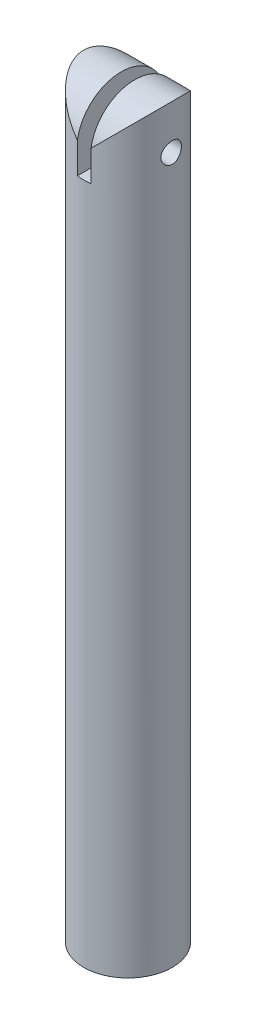
SolidWorks part; units mm, degrees
ref_plane "Front Plane" through (0, 0, 0) normal (0, 0, 1) x (1, 0, 0)
ref_plane "Top Plane" through (0, 0, 0) normal (0, 1, 0) x (1, 0, 0)
ref_plane "Right Plane" through (0, 0, 0) normal (1, 0, 0) x (0, 0, -1)
sketch "Sketch1" plane through (0, 0, 0) normal (0, 1, 0) x (1, 0, 0)
  circle A0 centre (0, 0) radius 2.5
  circle A1 centre (0, 0) radius 6.5
  dimension "D1" = 5
  dimension "D2" = 13
extrude "Boss-Extrude1" add sketch "Sketch1" along normal blind 100
sketch "Sketch2" plane through (0, 100, 0) normal (0, 1, 0) x (1, 0, 0)
  circle A0 centre (0, 0) radius 6.5
extrude "Boss-Extrude2" add sketch "Sketch2" against normal blind 10
sketch "Sketch3" plane through (0, 100, 0) normal (0, 1, 0) x (1, 0, 0)
  line L2 (-1, -6.4226) -> (-1, 6.4226)
  line L4 (1, -6.4226) -> (1, 6.4226)
  arc A0 (1, -6.4226) -> (1, 6.4226) centre (0, 0) ccw
  arc A2 (-1, 6.4226) -> (-1, -6.4226) centre (0, 0) ccw
  point P0 (0, 0)
extrude "Boss-Extrude3" add sketch "Sketch3" along normal blind 10
sketch "Sketch4" plane through (0, 0, 0) normal (1, 0, 0) x (0, 0, -1)
  line L0 (-6.5, 103.5) -> (6.5, 103.5)
  line L1 (6.4226, 110) -> (-6.4226, 110) construction
  line L2 (-6.5, 103.5) -> (-6.4226, 110)
  line L3 (-6.4226, 110) -> (6.4226, 110)
  line L4 (6.4226, 110) -> (6.5, 103.5)
  arc A0 (6.5, 103.5) -> (-6.5, 103.5) centre (0, 103.5) ccw
  dimension "D1" = 13
  dimension "D2" = 6.5
extrude "Cut-Extrude2" cut sketch "Sketch4" against normal through all and the other way through all contours A0 L4 L3 | A0 L3 L2
sketch "Sketch5" plane through (1, 0, 0) normal (-1, 0, 0) x (0, 0, 1)
  line L0 (-6.5, 100) -> (-6.5, 0) construction
  circle A0 centre (0, 103.5) radius 1.5
  arc A3 (6.4226, 104.5) -> (-6.4226, 104.5) centre (0, 103.5) ccw construction
  point P7 (0, 110)
  dimension "D3" = 3
  dimension "D1" = 6.5
  dimension "D2" = 6.5
extrude "Cut-Extrude3" cut sketch "Sketch5" against normal through all and the other way through all
